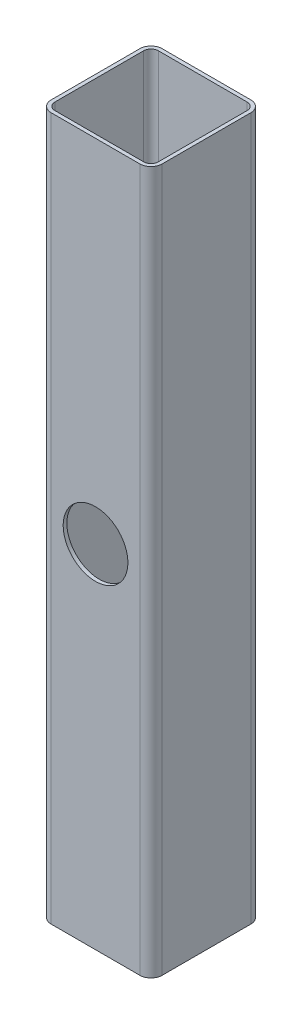
SolidWorks part; units mm, degrees
material "Plain Carbon Steel"
ref_plane "Front Plane" through (0, 0, 0) normal (0, 0, 1) x (1, 0, 0)
ref_plane "Top Plane" through (0, 0, 0) normal (0, 1, 0) x (1, 0, 0)
ref_plane "Right Plane" through (0, 0, 0) normal (1, 0, 0) x (0, 0, -1)
sketch "Sketch1" plane through (0, 0, 0) normal (0, 1, 0) x (1, 0, 0)
  line L1 (-24, -30) -> (24, -30)
  line L2 (-30, -24) -> (-30, 24)
  line L3 (-24, 30) -> (24, 30)
  line L4 (30, -24) -> (30, 24)
  line L5 (-30, -30) -> (30, 30) construction
  line L6 (-30, 30) -> (30, -30) construction
  arc A0 (30, -24) -> (24, -30) centre (24, -24) cw
  arc A1 (30, 24) -> (24, 30) centre (24, 24) ccw
  arc A2 (-24, 30) -> (-30, 24) centre (-24, 24) ccw
  arc A3 (-24, -30) -> (-30, -24) centre (-24, -24) cw
  point P0 (0, 0)
  dimension "D3" = 6
  dimension "D1" = 60
  dimension "D2" = 60
extrude "Boss-Extrude1" add sketch "Sketch1" along normal mid plane 380
shell "Shell1" thickness 2
sketch "Sketch2" plane through (0, 0, -30) normal (0, 0, -1) x (-1, 0, 0)
  line L1 (-15.5, 15.5) -> (15.5, 15.5)
  line L2 (-15.5, 15.5) -> (-15.5, -15.5)
  line L3 (-15.5, -15.5) -> (15.5, -15.5)
  line L4 (15.5, 15.5) -> (15.5, -15.5)
  line L5 (-15.5, 15.5) -> (15.5, -15.5) construction
  line L6 (-15.5, -15.5) -> (15.5, 15.5) construction
  point P0 (0, 0)
  dimension "D1" = 31
  dimension "D2" = 31
extrude "Cut-Extrude1" [suppressed] cut sketch "Sketch2" against normal through all
sketch "Sketch3" plane through (0, 0, -30) normal (0, 0, -1) x (-1, 0, 0)
  circle A0 centre (0, 0) radius 17.5
  dimension "D1" = 35
extrude "Cut-Extrude2" cut sketch "Sketch3" against normal through all
